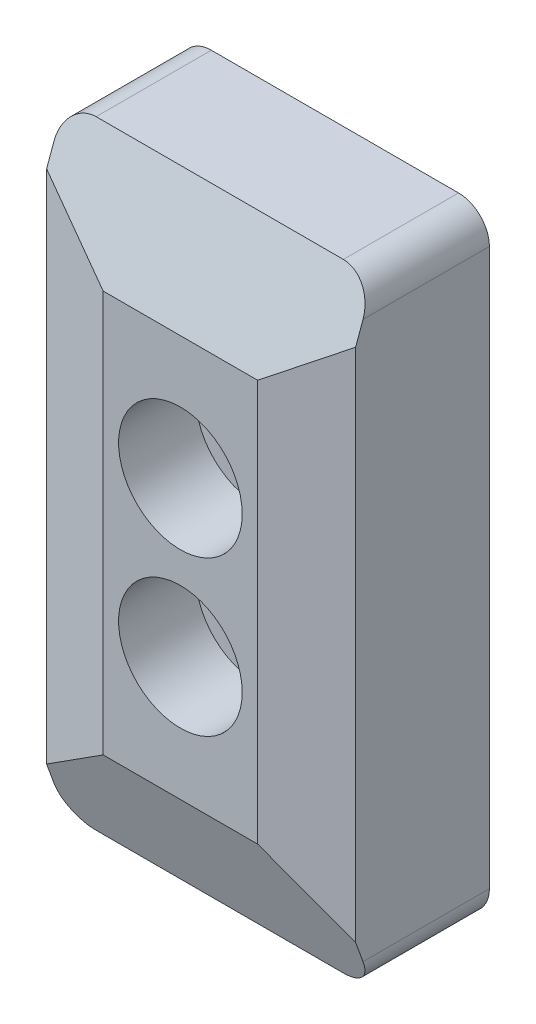
SolidWorks part; units mm, degrees
ref_plane "Front Plane" through (0, 0, 0) normal (0, 0, 1) x (1, 0, 0)
ref_plane "Top Plane" through (0, 0, 0) normal (0, 1, 0) x (1, 0, 0)
ref_plane "Right Plane" through (0, 0, 0) normal (1, 0, 0) x (0, 0, -1)
sketch "Sketch1" plane through (0, 0, 0) normal (0, 0, 1) x (1, 0, 0)
  line L0 (-10, -20) -> (-10, 20)
  line L1 (-10, -20) -> (10, -20)
  line L2 (-10, 20) -> (10, 20)
  line L3 (10, -20) -> (10, 20)
  line L4 (-10, -20) -> (10, 20) construction
  line L5 (-10, 20) -> (10, -20) construction
  line L6 (0, 5) -> (0, -5) construction
  circle A0 centre (0, -5) radius 2.15
  circle A1 centre (0, 5) radius 2.15
  point P1 (0, 0)
  point P12 (0, 0)
  point P14 (0, 0)
  point P15 (0, 0)
  point P17 (0, 0)
  point P22 (0, 0)
  dimension "D4" = 10
  dimension "D5" = 4.3
  dimension "D1" = 40
  dimension "D2" = 20
extrude "Boss-Extrude1" add sketch "Sketch1" along normal blind 10
chamfer "Chamfer1" distance 5 angle 15 2 edges at (10, 0, 10) (-10, 0, 10)
chamfer "Chamfer2" distance 7 angle 20 2 edges at (0, -20, 10) (0, 20, 10)
sketch "Sketch2" plane through (0, 0, 10) normal (0, 0, 1) x (1, 0, 0)
  circle A0 centre (0, 5) radius 4
  circle A1 centre (0, -5) radius 4
  dimension "D1" = 8
extrude "Cut-Extrude1" cut sketch "Sketch2" against normal blind 5
fillet "Fillet1" radius 2 4 edges at (-10, 20, 3.7261) (10, 20, 3.7261) (-10, -20, 3.7261) (10, -20, 3.7261)
